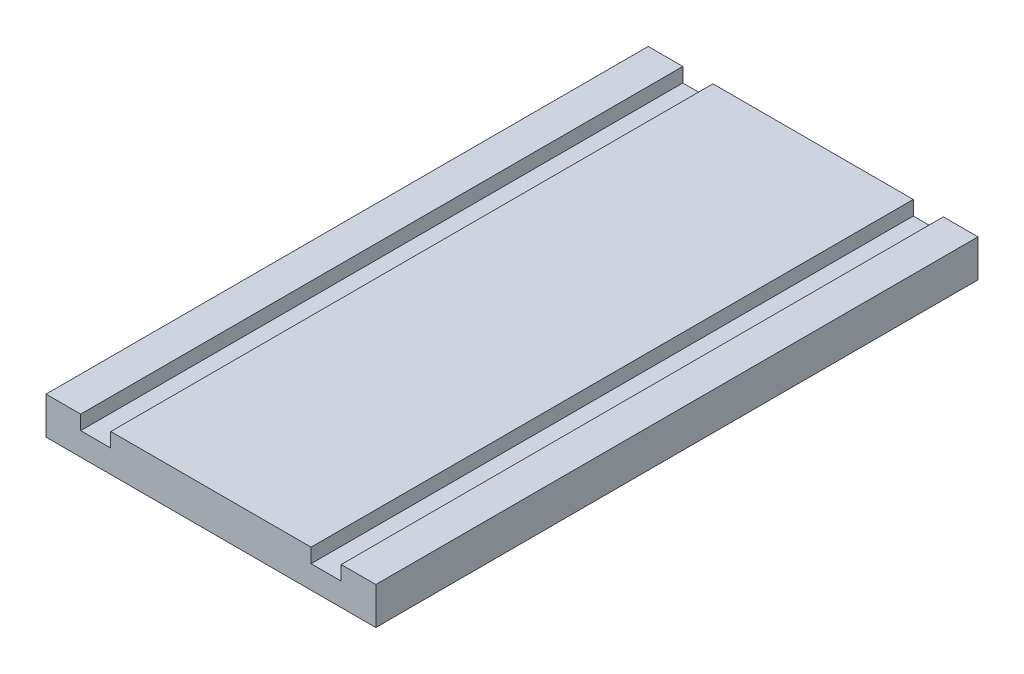
SolidWorks part; units mm, degrees
ref_plane "Front Plane" through (0, 0, 0) normal (0, 0, 1) x (1, 0, 0)
ref_plane "Top Plane" through (0, 0, 0) normal (0, 1, 0) x (1, 0, 0)
ref_plane "Right Plane" through (0, 0, 0) normal (1, 0, 0) x (0, 0, -1)
sketch "Sketch1" plane through (0, 0, 0) normal (0, 1, 0) x (1, 0, 0)
  line L1 (115, -210) -> (-115, -210)
  line L2 (115, -210) -> (115, 210)
  line L3 (115, 210) -> (-115, 210)
  line L4 (-115, -210) -> (-115, 210)
  line L5 (115, -210) -> (-115, 210) construction
  line L6 (115, 210) -> (-115, -210) construction
  point P0 (0, 0)
  dimension "D1" = 230
  dimension "D2" = 420
extrude "Boss-Extrude1" add sketch "Sketch1" along normal blind 26
sketch "Sketch2" plane through (0, 26, 0) normal (0, 1, 0) x (1, 0, 0)
  line L0 (0, 259.77) -> (0, 83.6843) construction
  line L1 (-69.85, 210) -> (-90.85, 210)
  line L2 (-69.85, 210) -> (-69.85, -210)
  line L3 (-69.85, -210) -> (-90.85, -210)
  line L4 (-90.85, 210) -> (-90.85, -210)
  line L5 (-69.85, 210) -> (-90.85, -210) construction
  line L6 (-69.85, -210) -> (-90.85, 210) construction
  line L7 (-80.35, 0) -> (0, 0) construction
  line L8 (115, 210) -> (-115, 210) construction
  line L9 (69.85, -210) -> (90.85, -210)
  line L10 (69.85, 210) -> (90.85, 210)
  line L11 (90.85, 210) -> (90.85, -210)
  line L12 (69.85, 210) -> (69.85, -210)
  point P0 (-80.35, 0)
  point P10 (-33.4737, 210)
  point P13 (-445.9256, 210)
  dimension "D1" = 21
  dimension "D2" = 139.7
extrude "Cut-Extrude1" cut sketch "Sketch2" against normal blind 10
sketch "Sketch3" plane through (0, 26, 0) normal (0, 1, 0) x (1, 0, 0)
  line L1 (-80.35, 210) -> (-80.35, -210) construction
  line L2 (-69.85, 210) -> (-90.85, 210) construction
  line L3 (-90.85, -210) -> (-69.85, -210) construction
  line L4 (80.35, -210) -> (80.35, 210) construction
  line L5 (69.85, -210) -> (90.85, -210) construction
  line L6 (90.85, 210) -> (69.85, 210) construction
  point P12 (69.85, 210)
  point P14 (-69.85, 210)
  dimension "D1" = 160.7
  dimension "D2" = 139.7
